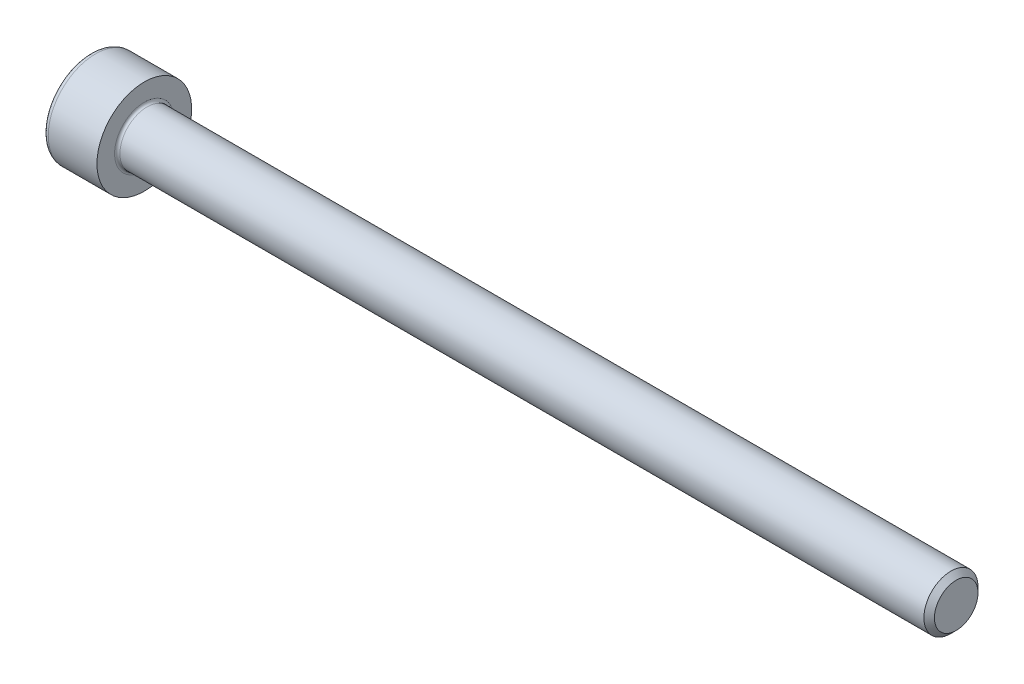
SolidWorks part; units mm, degrees
revolve "Base-Revolve" add sketch "BodySke"
sketch "BodySke" plane through (0, 0, 0) normal (0, 0, 1) x (1, 0, 0)
  line L0 (0, 0) -> (0, 3.5)
  line L1 (0, 3.5) -> (4, 3.5)
  line L2 (4, 3.5) -> (4, 2)
  line L3 (4, 2) -> (63.61, 2)
  line L4 (64, 1.61) -> (64, 0)
  line L5 (64, 0) -> (0, 0)
  line L6 (-31.75, 0) -> (127, 0) construction
  line L8 (64, 1.61) -> (63.61, 2)
  line L10 (64, -1.61) -> (63.61, -2) construction
  line L11 (4.7, 9.525) -> (4.7, 3.175) construction
  line L12 (44, 9.525) -> (44, 3.175) construction
  line L13 (4, 9.525) -> (4, 3.175) construction
  dimension "Head_ht" = 4
  dimension "Length" = 60
  dimension "Body_ch_ang" = 45
  dimension "Diameter" = 4
  dimension "Minor_dia" = 3.22
  dimension "Advance" = 0.7
  dimension "Thread_nom" = 20
  dimension "Thread_length" = 60
  dimension "Head_dia" = 7
cosmetic thread "ThreadCosmetic" [suppressed]
fillet "Fillet1" radius 0.2 1 edges at (4, 0, 2)
fillet "Fillet2" radius 0.4 1 edges at (0, 0, 3.5)
ref_plane "Plane1" through (0, 0, 0) normal (0, 0, 1) x (1, 0, 0)
ref_plane "Plane2" through (0, 0, 0) normal (0, 1, 0) x (1, 0, 0)
ref_plane "Plane3" through (0, 0, 0) normal (1, 0, 0) x (0, 0, -1)
sketch "Sketch2" plane through (0, 0, 0) normal (0, 0, 1) x (1, 0, 0)
  line L0 (0, 1.51) -> (2, 1.51)
  line L1 (2, 1.51) -> (2.8718, 0)
  line L2 (-31.75, 0) -> (127, 0) construction
  line L3 (2.8718, 0) -> (0, 0)
  line L4 (0, 0) -> (0, 1.51)
  line L6 (0, 0) -> (47.625, 0) construction
  dimension "D1" = 1.51
  dimension "D2" = 60
  dimension "Depth" = 2
revolve "Hex-PreBroach" cut sketch "Sketch2" angle 360 about L6
sketch "Sketch3" plane through (0, 0, 0) normal (-1, 0, 0) x (0, 0.5, 0.866)
  line L0 (0.8718, 1.51) -> (-0.8718, 1.51)
  line L1 (-0.8718, 1.51) -> (-1.7436, 0)
  line L2 (0.8718, 1.51) -> (1.7436, 0)
  line L3 (0.8718, -1.51) -> (1.7436, 0)
  line L4 (0.8718, -1.51) -> (-0.8718, -1.51)
  line L5 (-0.8718, -1.51) -> (-1.7436, 0)
  dimension "D1" = 1.51
  dimension "D2" = 1.51
  dimension "Hex_size" = 3.02
extrude "Hex" cut sketch "Sketch3" against normal blind 2
sketch "ThdSchSke" plane through (0, 0, 0) normal (0, 0, 1) x (1, 0, 0)
  line L0 (44, -1.61) -> (43.7269, -2)
  line L1 (44, -1.61) -> (44.2731, -2)
  line L2 (44.2731, -2) -> (44.2731, -2.5)
  line L3 (-3.175, 0) -> (5.1513, 0) construction
  line L4 (0, 3.1) -> (0, -3.1) construction
  line L5 (44.2731, -2.5) -> (43.7269, -2.5)
  line L6 (43.7269, -2.5) -> (43.7269, -2)
  dimension "Thread_minor" = 3.22
  dimension "Diameter" = 4
  dimension "Start" = 44
revolve "ThreadSchematic" [suppressed] cut sketch "ThdSchSke" angle 360 about L3
pattern_linear "ThdSchPat" [suppressed]
equation "\"D2@Sketch3\" = \"Hex_size@Sketch3\" / 2"
equation "\"D1@Sketch3\" = \"Hex_size@Sketch3\" / 2"
equation "\"D1@Sketch2\" = \"Hex_size@Sketch3\" / 2"
equation "\"Thread_minor@ThreadCosmetic\"  =  \"Minor_dia@BodySke\""
equation "\"Depth@Sketch2\" =  \"Key_eng@Hex\""
equation "\"Thread_length@ThreadCosmetic\" = ((sgn( (\"Length@BodySke\" - \"Advance@BodySke\" * 3.0) - \"Thread_nom@BodySke\" )-1)*( (\"Length@BodySke\" - \"Advance@BodySke\" * 3.0) - \"Thread_nom@BodySke\" ))/-2+ \"Thread_nom@BodySke\""
equation "\"Thread_minor@ThdSchSke\" = \"Minor_dia@BodySke\""
equation "\"Diameter@ThdSchSke\" = \"Diameter@BodySke\""
equation "\"Overcut@ThdSchSke\" = \"Diameter@BodySke\" * 1.25"
equation "\"Start@ThdSchSke\" = \"Head_ht@BodySke\" + \"Length@BodySke\" - \"Thread_length@ThreadCosmetic\"  '---Non-countersunk---"
equation "\"Num_threads@ThdSchPat\" = int( \"Thread_length@ThreadCosmetic\" / \"Advance@BodySke\" + 0.999 )  + 1"
equation "\"Advance@ThdSchPat\" = \"Thread_length@ThreadCosmetic\" /  (\"Num_threads@ThdSchPat\" - 1) 'relax it"
equation "\"Num_threads@ThdSchPat\" = \"Num_threads@ThdSchPat\" - sgn( \"Num_threads@ThdSchPat\" - 1) '---chamfered tips only---"
